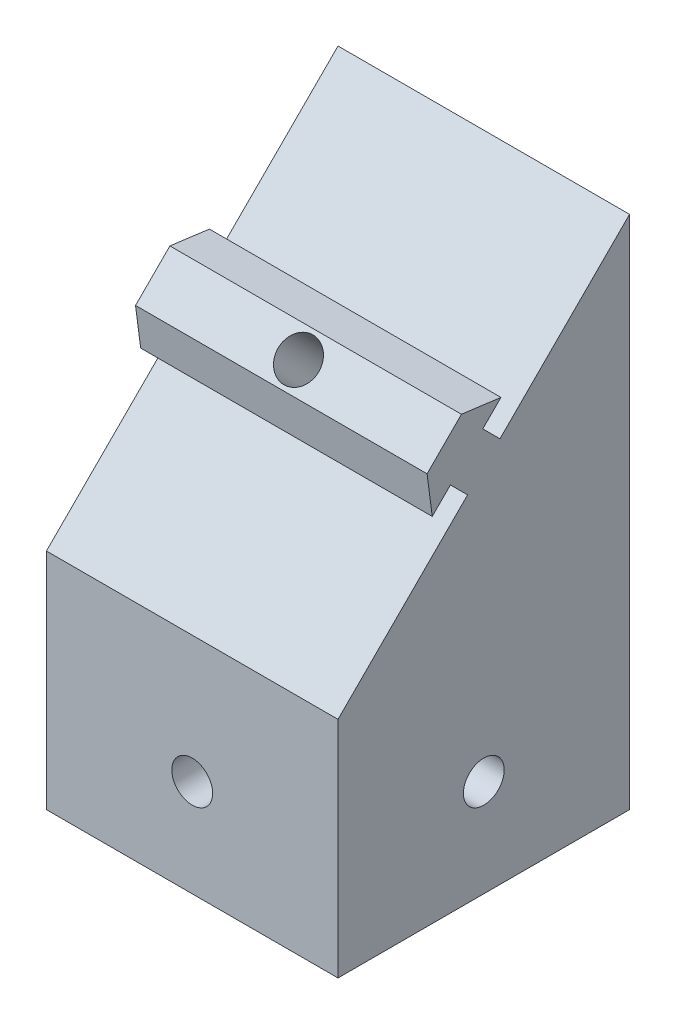
SolidWorks part; units mm, degrees
ref_plane "Front Plane" through (0, 0, 0) normal (0, 0, 1) x (1, 0, 0)
ref_plane "Top Plane" through (0, 0, 0) normal (0, 1, 0) x (1, 0, 0)
ref_plane "Right Plane" through (0, 0, 0) normal (1, 0, 0) x (0, 0, -1)
sketch "Sketch1" plane through (0, 0, 0) normal (0, 1, 0) x (1, 0, 0)
  line L0 (-15, -15) -> (-15, 15)
  line L1 (10, -10) -> (-10, -10)
  line L2 (10, -10) -> (10, 10)
  line L3 (10, 10) -> (-10, 10)
  line L4 (-10, -10) -> (-10, 10)
  line L5 (10, -10) -> (-10, 10) construction
  line L6 (10, 10) -> (-10, -10) construction
  line L7 (15, 15) -> (-15, 15)
  line L8 (15, -15) -> (15, 15)
  line L9 (15, -15) -> (-15, -15)
  point P0 (0, 0)
  dimension "D1" = 20
  dimension "D2" = 20
  dimension "D3" = 5
extrude "Boss-Extrude1" add sketch "Sketch1" along normal blind 20
sketch "Sketch2" plane through (0, 20, 0) normal (0, 1, 0) x (1, 0, 0)
  line L0 (4, -2.3365) -> (4, 2.6635)
  line L1 (8, -2.3555) -> (8, 2.3555)
  line L2 (8, -5.0498) -> (8, 4.9502)
  line L3 (10, -10) -> (10, 10) construction
  line L4 (4, 2.6635) -> (8, 4.9502)
  line L5 (4, -2.3365) -> (8, -5.0498)
  line L6 (8, -2.3555) -> (10, -2.3555)
  line L7 (8, 2.3555) -> (10, 2.3555)
  line L8 (10, 2.3555) -> (10, -2.3555)
  line L9 (-2.3365, -4) -> (-5.0498, -8)
  line L10 (-5.0498, -8) -> (4.9502, -8)
  line L11 (2.6635, -4) -> (4.9502, -8)
  line L12 (-2.3365, -4) -> (2.6635, -4)
  line L13 (2.3555, -10) -> (-2.3555, -10)
  line L14 (-2.3555, -8) -> (-2.3555, -10)
  line L15 (-2.3555, -8) -> (2.3555, -8)
  line L16 (2.3555, -8) -> (2.3555, -10)
  line L17 (-4, 2.3365) -> (-8, 5.0498)
  line L18 (-8, 5.0498) -> (-8, -4.9502)
  line L19 (-4, -2.6635) -> (-8, -4.9502)
  line L20 (-4, 2.3365) -> (-4, -2.6635)
  line L21 (-10, -2.3555) -> (-10, 2.3555)
  line L22 (-8, 2.3555) -> (-10, 2.3555)
  line L23 (-8, 2.3555) -> (-8, -2.3555)
  line L24 (-8, -2.3555) -> (-10, -2.3555)
  line L25 (2.3365, 4) -> (5.0498, 8)
  line L26 (5.0498, 8) -> (-4.9502, 8)
  line L27 (-2.6635, 4) -> (-4.9502, 8)
  line L28 (2.3365, 4) -> (-2.6635, 4)
  line L29 (-2.3555, 10) -> (2.3555, 10)
  line L30 (2.3555, 8) -> (2.3555, 10)
  line L31 (2.3555, 8) -> (-2.3555, 8)
  line L32 (-2.3555, 8) -> (-2.3555, 10)
  point P3 (4, 0.1635)
  point P6 (8, 0)
  point P9 (8, -0.0498)
  point P40 (0, 0)
  line M9 (-10, 10) -> (10, 10)
  line M10 (10, 10) -> (10, -10)
  line M11 (10, -10) -> (-10, -10)
  dimension "D1" = 2
  dimension "D2" = 10
  dimension "D3" = 5
  dimension "D4" = 0
  dimension "D5" = 4
  dimension "D7" = 4.711
  dimension "D6" = 4
extrude "Boss-Extrude2" add sketch "Sketch2" against normal blind 20 separate body contours L28 L25 L26 L27 | L32 L26 L30 M9 | L20 L17 L18 L19 | L12 L9 L10 L11 | L16 L10 L14 M11 | L0 L5 L2 L1 L4 | L7 L1 L6 M10 | L21 L22 L23 L24
sketch "Sketch3" plane through (-15, 0, 0) normal (-1, 0, 0) x (0, 0, 1)
  circle A0 centre (0, 10) radius 2.1
  dimension "D1" = 4.2
extrude "Cut-Extrude1" cut sketch "Sketch3" against normal through all
sketch "Sketch4" plane through (0, 0, -15) normal (0, 0, -1) x (-1, 0, 0)
  circle A0 centre (0, 10) radius 2.1
  dimension "D1" = 4.2
extrude "Cut-Extrude2" cut sketch "Sketch4" against normal through all
sketch "Sketch5" plane through (15, 0, 0) normal (1, 0, 0) x (0, 0, -1)
  line L0 (-15, 20) -> (15, 50)
  line L1 (-15, 20) -> (15, 20) construction
  line L2 (-15, 20) -> (-15, 23.0499)
  line L3 (-15, 23.0499) -> (15, 53.0499)
  line L4 (15, 53.0499) -> (15, 50)
  line L5 (15, 20) -> (15, 0) construction
  line L6 (15, 53.0499) -> (15, 20)
  line L7 (15, 50) -> (15, 20)
  line L8 (-15, 20) -> (15, 20)
  line M8 (15, 20) -> (-15, 20)
  dimension "D1" = 45
  dimension "D2" = 0
extrude "Boss-Extrude3" add sketch "Sketch5" against normal blind 30 contours L4 L3 L2 L0 | L6 L0 M8
ref_plane "Plane1" through (15, 0, 0) normal (1, 0, 0) x (0, 0.7071, -0.7071)
sketch "Sketch8" plane through (15, 0, 0) normal (1, 0, 0) x (0, 0.7071, -0.7071)
  line L0 (24.4053, 32.6553) -> (29.4053, 32.6553)
  line L1 (24.5498, 29.4053) -> (29.2608, 29.4053)
  line L2 (21.9053, 29.4053) -> (31.9053, 29.4053)
  line L3 (29.4053, 32.6553) -> (31.9053, 29.4053)
  line L4 (24.4053, 32.6553) -> (21.9053, 29.4053)
  line L5 (24.5498, 29.4053) -> (24.5498, 26.9053)
  line L6 (29.2608, 29.4053) -> (29.2608, 26.9053)
  line L7 (29.2608, 26.9053) -> (24.5498, 26.9053)
  line L14 (5.6921, 26.9053) -> (48.1185, 26.9053) construction
  point P2 (26.9053, 32.6553)
  point P5 (26.9053, 29.4053)
  point P8 (26.9053, 29.4053)
  point P11 (26.9053, 26.9053)
  point P14 (26.9053, 26.9053)
  dimension "D1" = 2.6445
  dimension "D2" = 4.711
  dimension "D3" = 10
  dimension "D4" = 5
  dimension "D5" = 3.25
  dimension "D6" = 0
extrude "Boss-Extrude4" add sketch "Sketch8" against normal blind 30 contours L0 L4 L2 L1 L3 | L7 L6 L1 L5
sketch "Sketch10" plane through (0, 23.0908, 23.0908) normal (0, 0.7071, 0.7071) x (1, 0, 0)
  circle A0 centre (0, 26.9053) radius 2.1
  dimension "D1" = 4.2
extrude "Cut-Extrude4" cut sketch "Sketch10" against normal through all
